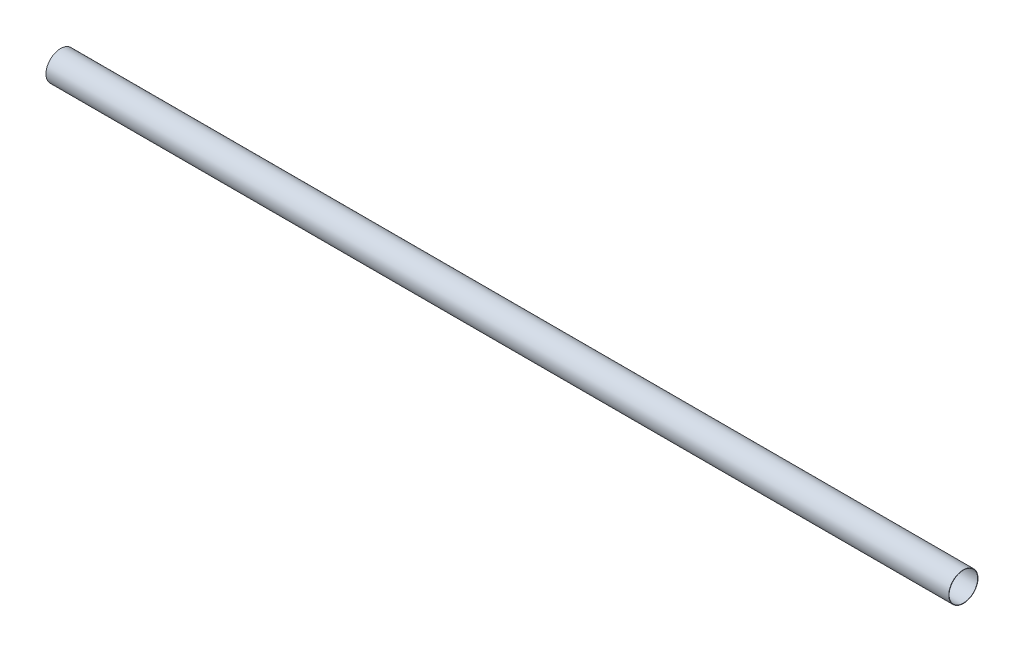
SolidWorks part; units mm, degrees
ref_plane "Front Plane" through (0, 0, 0) normal (0, 0, 1) x (1, 0, 0)
ref_plane "Top Plane" through (0, 0, 0) normal (0, 1, 0) x (1, 0, 0)
ref_plane "Right Plane" through (0, 0, 0) normal (1, 0, 0) x (0, 0, -1)
sketch "Sketch1" plane through (0, 0, 0) normal (1, 0, 0) x (0, 0, -1)
  circle A0 centre (0, 0) radius 40.5
  circle A1 centre (0, 0) radius 39.5
  dimension "D1" = 81
  dimension "D2" = 1
extrude "Boss-Extrude1" add sketch "Sketch1" along normal blind 2500
